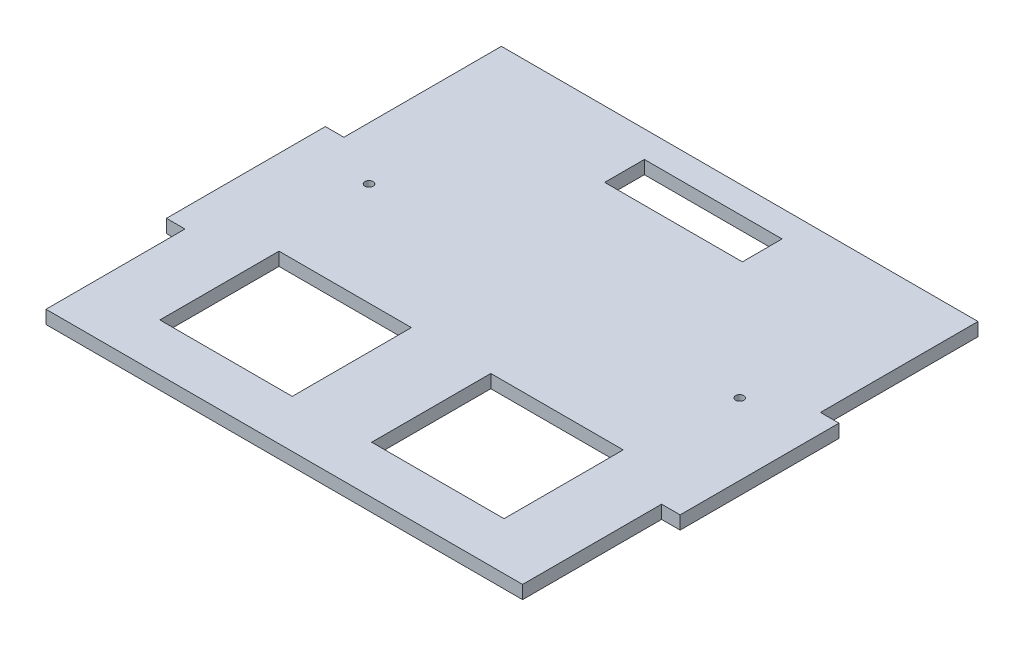
SolidWorks part; units mm, degrees
ref_plane "Front Plane" through (0, 0, 0) normal (0, 0, 1) x (1, 0, 0)
ref_plane "Top Plane" through (0, 0, 0) normal (0, 1, 0) x (1, 0, 0)
ref_plane "Right Plane" through (0, 0, 0) normal (1, 0, 0) x (0, 0, -1)
sketch "Sketch1" plane through (0, 0, 0) normal (0, 1, 0) x (1, 0, 0)
  line L0 (90, 30) -> (97, 30)
  line L1 (-90, -82.5) -> (90, -82.5)
  line L4 (90, -82.5) -> (90, -30)
  line L5 (-90, 89.5) -> (90, 89.5)
  line L7 (97, 30) -> (97, -30)
  line L8 (97, -30) -> (90, -30)
  line L9 (-93.4311, 0) -> (93.4311, 0) construction
  line L10 (0, -107.9144) -> (0, 107.9144) construction
  line L11 (90, 89.5) -> (90, 30)
  line L12 (-90, -82.5) -> (-90, -30)
  line L13 (-97, -30) -> (-90, -30)
  line L14 (-97, 30) -> (-97, -30)
  line L15 (-90, 30) -> (-97, 30)
  line L16 (-90, 89.5) -> (-90, 30)
  line L18 (-26, 64.5) -> (26, 64.5)
  line L19 (-26, 64.5) -> (-26, 79.5)
  line L20 (-26, 79.5) -> (26, 79.5)
  line L21 (26, 64.5) -> (26, 79.5)
  line L22 (-26, 64.5) -> (26, 79.5) construction
  line L23 (-26, 79.5) -> (26, 64.5) construction
  line L28 (15, -19.5) -> (65, -64.5) construction
  line L29 (-15, -64.5) -> (-65, -64.5)
  line L33 (-15, -64.5) -> (-15, -19.5)
  line L34 (-15, -19.5) -> (-65, -19.5)
  line L35 (-65, -64.5) -> (-65, -19.5)
  line L36 (-15, -64.5) -> (-65, -19.5) construction
  line L37 (-15, -19.5) -> (-65, -64.5) construction
  line L38 (15, -64.5) -> (65, -19.5) construction
  line L39 (15, -19.5) -> (65, -19.5)
  line L40 (65, -64.5) -> (65, -19.5)
  line L41 (15, -64.5) -> (65, -64.5)
  line L42 (15, -64.5) -> (15, -19.5)
  circle A0 centre (70, 19.5) radius 1.55
  circle A1 centre (-70, 19.5) radius 1.55
  point P0 (0, 0)
  point P13 (0, 0)
  point P16 (0, 0)
  point P20 (0, 72)
  point P26 (-40, -42)
  dimension "D14" = 3.1
  dimension "D15" = 20
  dimension "D1" = 30
  dimension "D2" = 180
  dimension "D3" = 7
  dimension "D4" = 60
  dimension "D5" = 82.5
  dimension "D6" = 52
  dimension "D7" = 15
  dimension "D8" = 0
  dimension "D9" = 50
  dimension "D10" = 45
  dimension "D11" = 15
  dimension "D12" = 18
  dimension "D13" = 10
  dimension "D16" = 70
extrude "Boss-Extrude1" add sketch "Sketch1" along normal blind 5
